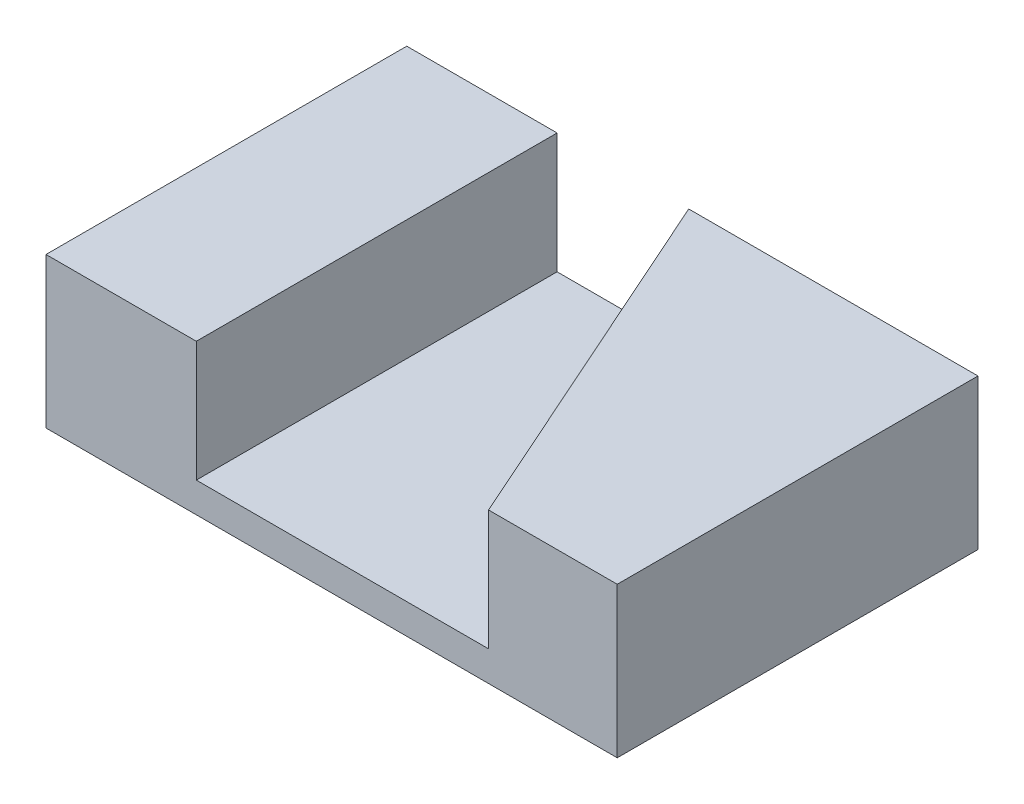
SolidWorks part; units mm, degrees
ref_plane "Спереди" through (0, 0, 0) normal (0, 0, 1) x (1, 0, 0)
ref_plane "Сверху" through (0, 0, 0) normal (0, 1, 0) x (1, 0, 0)
ref_plane "Справа" through (0, 0, 0) normal (1, 0, 0) x (0, 0, -1)
sketch "Эскиз3" plane through (0, 0, 0) normal (0, 1, 0) x (1, 0, 0)
  line L1 (0, 0) -> (19, 0)
  line L2 (0, 0) -> (0, 12)
  line L3 (0, 12) -> (19, 12)
  line L4 (19, 0) -> (19, 12)
  dimension "D1" = 19
  dimension "D2" = 12
extrude "Бобышка-Вытянуть1" add sketch "Эскиз3" along normal blind 5
hole_wizard "Отверстие обработанное метчиком M2x0.42" positions "Эскиз9" profile "Эскиз8" tap size "M2x0.4" standard "Ansi (метрические)" end condition through all
sketch "Эскиз9" plane through (0, 0, -12) normal (0, 0, -1) x (-1, 0, 0)
  line L0 (-19, 5) -> (0, 5) construction
  line L1 (0, 5) -> (0, 0) construction
  point P0 (-12, 3)
  dimension "D1" = 2
  dimension "D2" = 12
sketch "Эскиз8" plane through (12, 3, -12) normal (1, 0, 0) x (0, 1, 0)
  line L0 (0, 0) -> (0, 12)
  line L1 (0, 12) -> (1.025, 12)
  line L2 (0.8, 11.8425) -> (0.8, 0.1575)
  line L3 (0.8, 0.1575) -> (1.025, 0)
  line L5 (1.025, 0) -> (0, 0)
  line L6 (-0.8, 0.1575) -> (-1.025, 0) construction
  line L7 (1.025, 12) -> (0.8, 11.8425)
  line L8 (-1.025, 12) -> (-0.8, 11.8425) construction
  line L11 (0, -6.35) -> (0, 107.95) construction
  dimension "Диаметр проходного сверла" = 1.6
  dimension "Глубина проходного сверла" = 12
  dimension "Диаметр передней зенковки" = 2.05
  dimension "Угол передней зенковки" = 110
  dimension "Диаметр задней зенковки" = 2.05
  dimension "Угол задней зенковки" = 110
cosmetic thread "Отверстие резьбы2" parameters "D2"=2
hole_wizard "Отверстие с зазором M23" positions "Эскиз11" profile "Эскиз10" hole size "M2" standard "Ansi (метрические)"
sketch "Эскиз11" plane through (0, 0, 0) normal (0, 0, 1) x (1, 0, 0)
  circle A0 centre (12, 3) radius 0.8 construction
  point P0 (12, 3)
sketch "Эскиз10" plane through (12, 3, 0) normal (1, 0, 0) x (0, -1, 0)
  line L0 (0, 0) -> (0, 8.6309)
  line L1 (0, 8.6309) -> (1.05, 8)
  line L2 (1.05, 8) -> (1.05, 0)
  line L5 (1.05, 0) -> (0, 0)
  line L10 (0, 8.6309) -> (-1.05, 8) construction
  line L11 (0, -6.35) -> (0, 107.95) construction
  dimension "Диаметр отверстия" = 2.1
  dimension "Глубина отверстия" = 8
  dimension "Угол заточки сверла" = 118
sketch "Эскиз4" plane through (0, 5, 0) normal (0, 1, 0) x (1, 0, 0)
  line L0 (5, 12) -> (5, 0)
  line L1 (19, 12) -> (0, 12) construction
  line L2 (0, 0) -> (19, 0) construction
  line L3 (5, 0) -> (14.7213, 0)
  line L4 (14.7213, 0) -> (9.3785, 12)
  line L5 (9.3785, 12) -> (5, 12)
  line L6 (0, 12) -> (0, 0) construction
  dimension "D1" = 5
  dimension "D2" = 24
  dimension "D3" = 4
extrude "Вырез-Вытянуть1" cut sketch "Эскиз4" against normal blind 4
